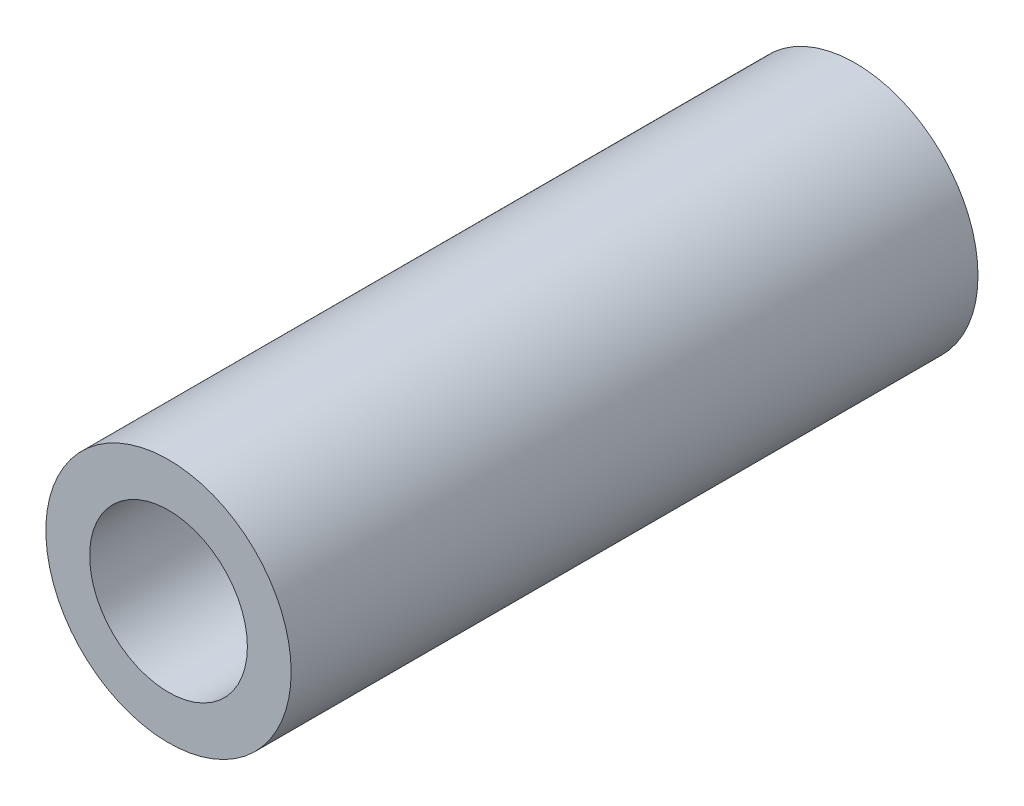
SolidWorks part; units mm, degrees
material "Nylon 101"
ref_plane "Front Plane" through (0, 0, 0) normal (0, 0, 1) x (1, 0, 0)
ref_plane "Top Plane" through (0, 0, 0) normal (0, 1, 0) x (1, 0, 0)
ref_plane "Right Plane" through (0, 0, 0) normal (1, 0, 0) x (0, 0, -1)
sketch "Sketch1" plane through (0, 0, 0) normal (0, 0, 1) x (1, 0, 0)
  circle A0 centre (0, 0) radius 3.9688
  circle A1 centre (0, 0) radius 2.5527
  dimension "D1" = 7.9375
  dimension "D2" = 5.1054
extrude "Boss-Extrude1" add sketch "Sketch1" along normal blind 22.225
